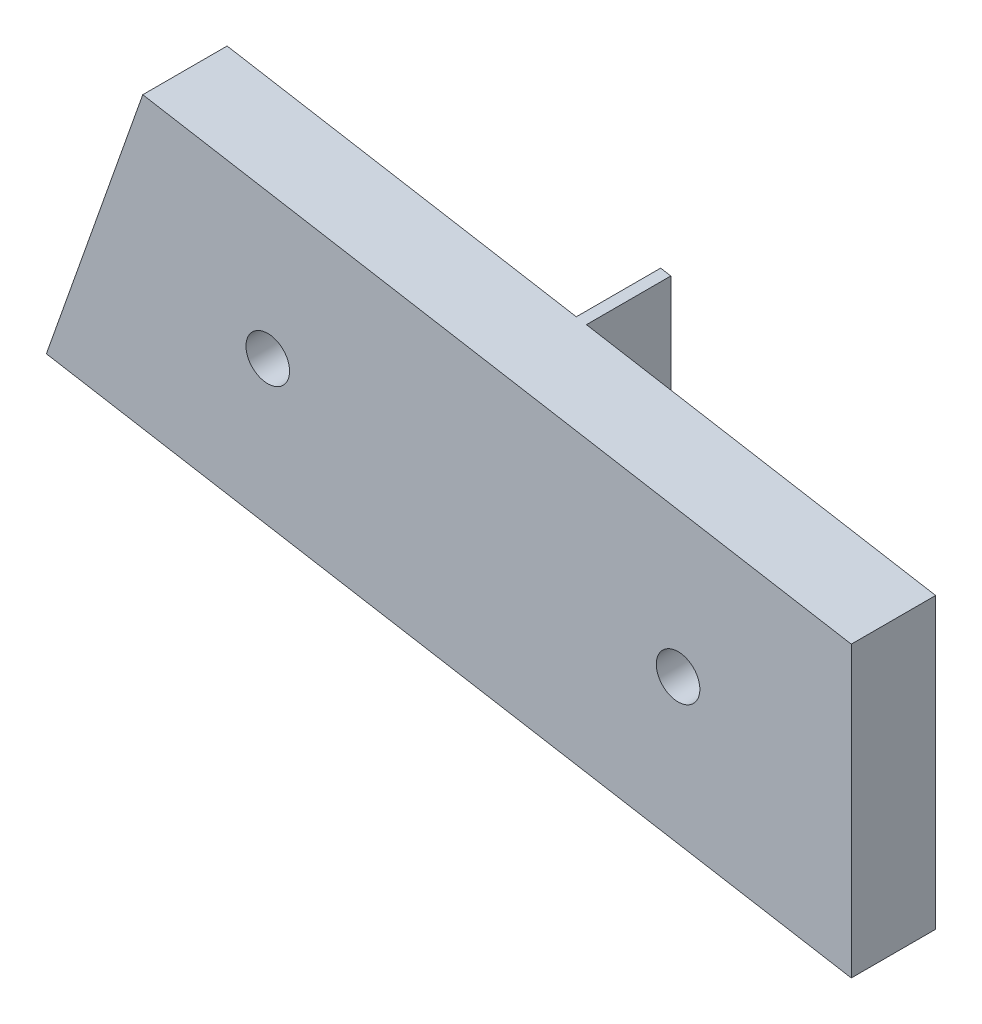
SolidWorks part; units mm, degrees
ref_plane "Спереди" through (0, 0, 0) normal (0, 0, 1) x (1, 0, 0)
ref_plane "Сверху" through (0, 0, 0) normal (0, 1, 0) x (1, 0, 0)
ref_plane "Справа" through (0, 0, 0) normal (1, 0, 0) x (0, 0, -1)
sketch "Эскиз1" plane through (0, 0, 0) normal (0, 0, 1) x (1, 0, 0)
  line L0 (-114.3235, 125.814) -> (-171.5752, 135.6387)
  line L1 (-171.5752, 135.6387) -> (-164.7191, 155.0267)
  line L2 (-164.7191, 155.0267) -> (-114.3235, 146.3785)
  line L3 (-114.3235, 146.3785) -> (-114.3235, 125.814)
extrude "Бобышка-Вытянуть1" add sketch "Эскиз1" along normal blind 6
sketch "Эскиз2" plane through (0, 0, 0) normal (0, 0, -1) x (-1, 0, 0)
  line L0 (146.7382, 131.3765) -> (139.1604, 130.0761)
  line L1 (171.5752, 135.6387) -> (114.3235, 125.814) construction
  line L2 (139.1604, 130.0761) -> (139.1604, 150.6407)
  line L3 (114.3235, 146.3785) -> (164.7191, 155.0267) construction
  line L4 (139.1604, 150.6407) -> (139.8822, 150.7645)
  line L5 (139.8822, 150.7645) -> (146.7382, 131.3765)
  dimension "D1" = 25.2
  dimension "D2" = 25.2
  dimension "D3" = 25.2
  dimension "D4" = 25.2
extrude "Бобышка-Вытянуть2" add sketch "Эскиз2" along normal blind 6
sketch "Эскиз3" plane through (0, 0, 0) normal (0, 0, -1) x (-1, 0, 0)
  circle A0 centre (126.6434, 138.2104) radius 1.55
  circle A1 centre (155.8273, 143.2185) radius 1.55
extrude "Вырез-Вытянуть1" cut sketch "Эскиз3" against normal blind 6
